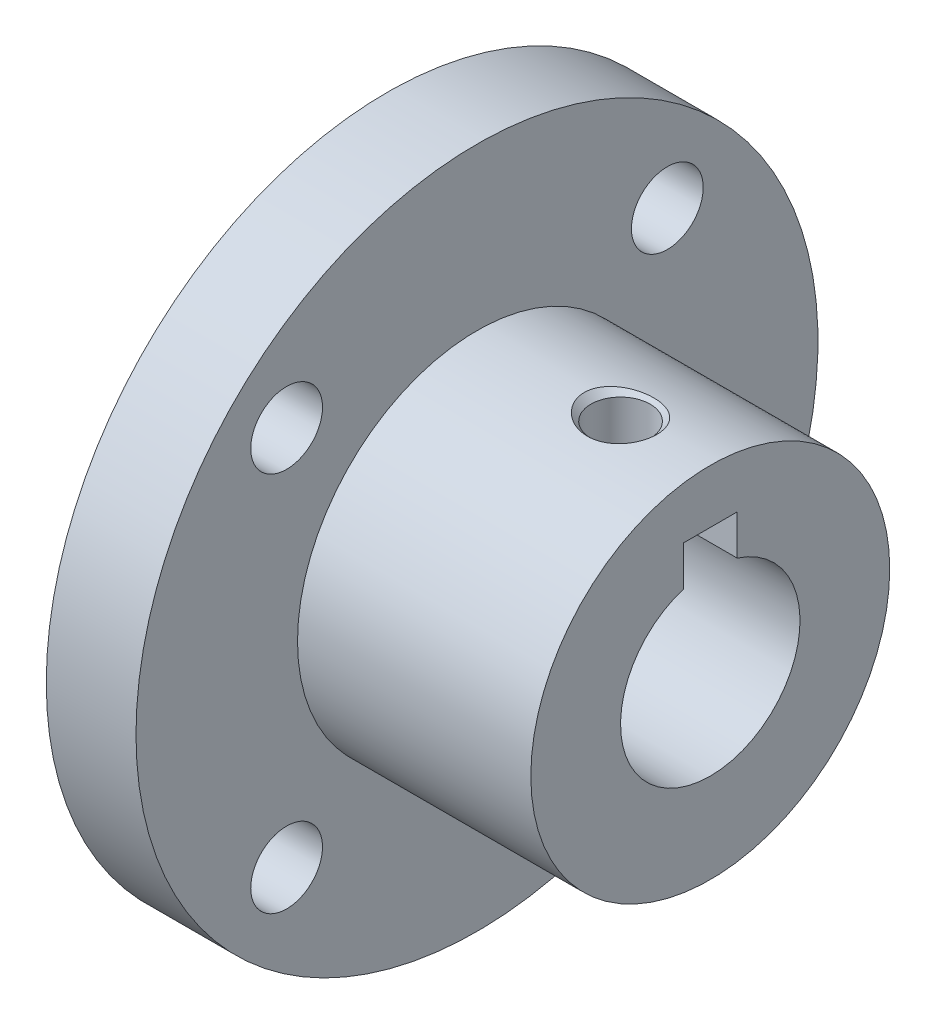
SolidWorks part; units mm, degrees
ref_plane "Piano frontale" through (0, 0, 0) normal (0, 0, 1) x (1, 0, 0)
ref_plane "Piano superiore" through (0, 0, 0) normal (0, 1, 0) x (1, 0, 0)
ref_plane "Piano destro" through (0, 0, 0) normal (1, 0, 0) x (0, 0, -1)
sketch "Sketch1" plane through (0, 0, 0) normal (1, 0, 0) x (0, 0, -1)
  circle A0 centre (0, 0) radius 10
  dimension "D1" = 20
extrude "SmallRing" add sketch "Sketch1" along normal blind 13
sketch "Sketch4" plane through (0, 0, 0) normal (-1, 0, 0) x (0, 0, 1)
  line L0 (-10.6066, 10.6066) -> (10.6066, 10.6066) construction
  line L5 (-10.6066, -10.6066) -> (10.6066, -10.6066) construction
  line L6 (-10.6066, -10.6066) -> (10.6066, 10.6066) construction
  line L7 (10.6066, 10.6066) -> (10.6066, -10.6066) construction
  line L8 (10.6066, -10.6066) -> (-10.6066, 10.6066) construction
  line L9 (-10.6066, 10.6066) -> (-10.6066, -10.6066) construction
  circle A0 centre (0, 0) radius 19
  circle A1 centre (0, 0) radius 15 construction
  circle A4 centre (-10.6066, 10.6066) radius 2
  circle A5 centre (10.6066, 10.6066) radius 2
  circle A6 centre (10.6066, -10.6066) radius 2
  circle A7 centre (-10.6066, -10.6066) radius 2
  dimension "D1" = 38
  dimension "D2" = 4
  dimension "D3" = 30
extrude "BigRing" add sketch "Sketch4" along normal blind 5
sketch "Sketch34" plane through (13, 0, 0) normal (1, 0, 0) x (0, 0, -1)
  line L0 (0, 10) -> (0, 0) construction
  circle A0 centre (0, 0) radius 10 construction
hole_wizard "M4 Tapped Hole1" positions "3DSketch3" profile "Sketch36" tap size "M4" standard "ISO"
sketch3d "3DSketch3"
  line L0 (13, 10, 0) -> (0, 10, 0) construction
  circle A0 centre (0, 0, 0) radius 10 construction
  point P0 (8, 10, 0)
  point P6 (10, 0, 0)
  dimension "D1" = 5
sketch "Sketch36" plane through (8, 10, 0) normal (1, 0, 0) x (0, 0, 1)
  line L0 (0, 0) -> (0, 11.0914)
  line L1 (0, 11.0914) -> (1.65, 10.1)
  line L2 (1.65, 10.1) -> (1.65, 0.375)
  line L3 (1.65, 0.375) -> (2.025, 0)
  line L5 (2.025, 0) -> (0, 0)
  line L6 (-1.65, 0.375) -> (-2.025, 0) construction
  line L10 (0, 11.0914) -> (-1.65, 10.1) construction
  line L11 (0, -6.35) -> (0, 107.95) construction
  dimension "Tap Drill Dia." = 3.3
  dimension "Tap Drill Depth" = 10.1
  dimension "Near C'Sink Dia." = 4.05
  dimension "Near C'Sink Angle" = 90
  dimension "Drill Angle" = 118
sketch "Sketch42" plane through (13, 0, 0) normal (1, 0, 0) x (0, 0, -1)
  circle A0 centre (0, 0) radius 5
  dimension "D1" = 10
extrude "Motor Shaft Hole" cut sketch "Sketch42" against normal blind 20
sketch "Sketch43" plane through (13, 0, 0) normal (1, 0, 0) x (0, 0, -1)
  line L0 (1.5, 7) -> (-1.5, 3) construction
  line L1 (1.5, 7) -> (-1.5, 7)
  line L2 (1.5, 7) -> (1.5, 3)
  line L3 (1.5, 3) -> (-1.5, 3)
  line L4 (-1.5, 7) -> (-1.5, 3)
  line L5 (1.5, 3) -> (-1.5, 7) construction
  line L6 (0, 0) -> (0, 5) construction
  line L7 (0, 10) -> (0, 0) construction
  circle A0 centre (0, 0) radius 5 construction
  circle A2 centre (0, 0) radius 5 construction
  point P4 (0, 5)
  point P11 (0, 5)
  point P17 (1.5, 4.7697)
  dimension "D2" = 3
  dimension "D3" = 4
  dimension "D4" = 2.2303
  dimension "D5" = 1.7697
extrude "Keyway" cut sketch "Sketch43" against normal blind 18
